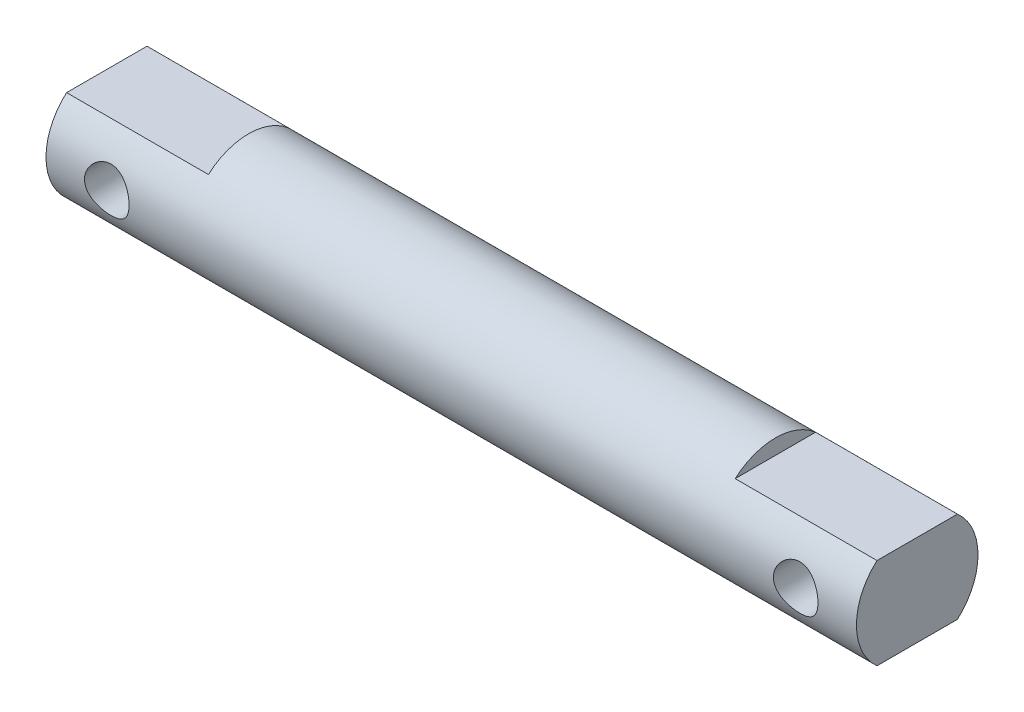
SolidWorks part; units mm, degrees
material "Plain Carbon Steel"
ref_plane "Front Plane" through (0, 0, 0) normal (0, 0, 1) x (1, 0, 0)
ref_plane "Top Plane" through (0, 0, 0) normal (0, 1, 0) x (1, 0, 0)
ref_plane "Right Plane" through (0, 0, 0) normal (1, 0, 0) x (0, 0, -1)
sketch "Sketch1" plane through (0, 0, 0) normal (0, 0, 1) x (1, 0, 0)
  line L0 (0, 0) -> (45.9529, 0) construction
  line L1 (-20, 3) -> (20, 3)
  line L2 (-20, 3) -> (-20, 0)
  line L3 (-20, 0) -> (20, 0)
  line L4 (20, 3) -> (20, 0)
  line L5 (0, 0) -> (0, 22.8572) construction
  line L6 (-13, 3) -> (-13, 0) construction
  line L7 (13, 3) -> (13, 0) construction
  dimension "D1" = 6
  dimension "D2" = 26
  dimension "D3" = 7
revolve "Revolve1" add sketch "Sketch1" angle 360 about L0
sketch "Sketch2" plane through (0, 0, 0) normal (0, 0, 1) x (1, 0, 0)
  line L0 (0, 0) -> (-31.5706, 0) construction
  line L1 (-20, 3) -> (-13, 3)
  line L2 (-20, 3) -> (-20, 2.25)
  line L3 (-20, 2.25) -> (-13, 2.25)
  line L4 (-13, 3) -> (-13, 2.25)
  line L5 (-20, -2.25) -> (-13, -2.25)
  line L6 (-20, -2.25) -> (-20, -3)
  line L7 (-20, -3) -> (-13, -3)
  line L8 (-13, -2.25) -> (-13, -3)
  line L9 (13, 3) -> (20, 3)
  line L10 (13, 3) -> (13, 2.25)
  line L11 (13, 2.25) -> (20, 2.25)
  line L12 (20, 3) -> (20, 2.25)
  line L13 (20, -2.25) -> (13, -2.25)
  line L14 (20, -2.25) -> (20, -3)
  line L15 (20, -3) -> (13, -3)
  line L16 (13, -2.25) -> (13, -3)
  line L17 (-20, 3) -> (-20, -3) construction
  line L18 (20, -3) -> (20, 3) construction
  line L19 (20, 3) -> (-20, 3) construction
  line L20 (-20, -3) -> (20, -3) construction
  dimension "D1" = 4.5
  dimension "D2" = 7
extrude "Cut-Extrude1" cut sketch "Sketch2" against normal through all and the other way through all
sketch "Sketch3" plane through (0, 0, 0) normal (0, 0, 1) x (1, 0, 0)
  line L0 (17, 0) -> (20, 0) construction
  line L1 (20, -2.25) -> (20, 2.25) construction
  line L2 (-17, 0) -> (-20, 0) construction
  line L3 (-20, 2.25) -> (-20, -2.25) construction
  circle A0 centre (-17, 0) radius 1.1
  circle A1 centre (17, 0) radius 1.1
  dimension "D1" = 2.2
  dimension "D2" = 3
extrude "Cut-Extrude2" cut sketch "Sketch3" against normal through all and the other way through all
